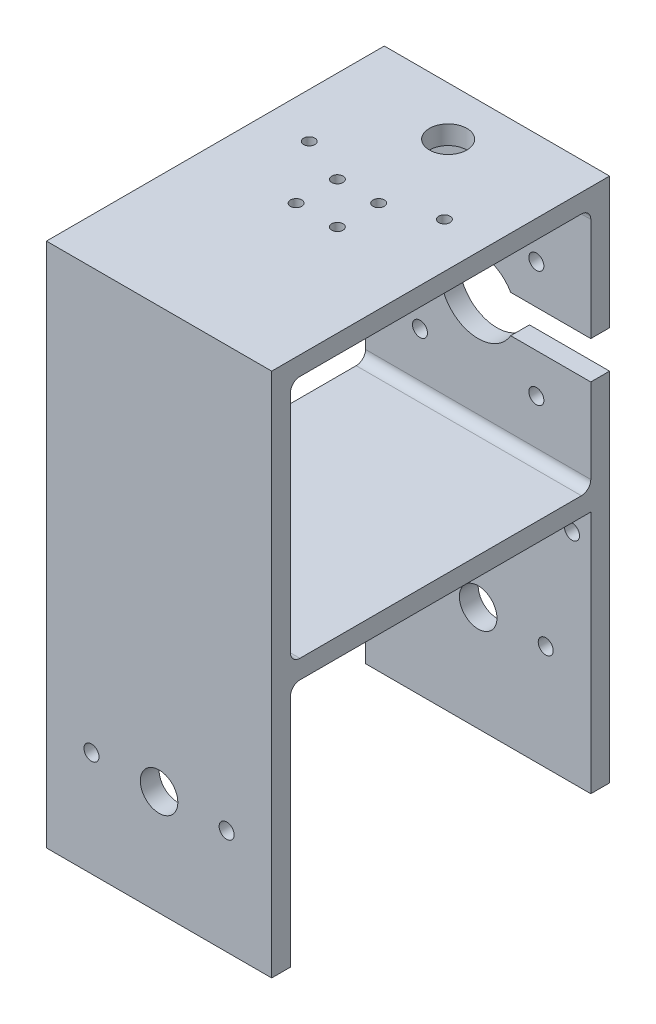
SolidWorks part; units mm, degrees
ref_plane "Front Plane" through (0, 0, 0) normal (0, 0, 1) x (1, 0, 0)
ref_plane "Top Plane" through (0, 0, 0) normal (0, 1, 0) x (1, 0, 0)
ref_plane "Right Plane" through (0, 0, 0) normal (1, 0, 0) x (0, 0, -1)
sketch "Sketch1" plane through (0, 0, 0) normal (1, 0, 0) x (0, 0, -1)
  line L0 (0, 0) -> (0, -140)
  line L1 (0, -140) -> (-5, -140)
  line L2 (-5, -140) -> (-5, -75)
  line L3 (-5, -75) -> (-85, -75)
  line L4 (-85, -75) -> (-85, -140)
  line L5 (-85, -140) -> (-90, -140)
  line L6 (-90, -140) -> (-90, 0)
  line L7 (-90, 0) -> (0, 0)
  dimension "D1" = 90
  dimension "D2" = 80
  dimension "D3" = 5
  dimension "D4" = 80
  dimension "D5" = 65
  dimension "D6" = 65
  dimension "D7" = 75
  dimension "D8" = 140
  dimension "D9" = 5
extrude "Boss-Extrude1" add sketch "Sketch1" against normal blind 60
sketch "Sketch2" plane through (0, 0, 0) normal (1, 0, 0) x (0, 0, -1)
  line L0 (-85, -75) -> (-5, -75) construction
  line L1 (-85, -70) -> (-5, -70)
  line L2 (-85, -70) -> (-85, -5)
  line L3 (-85, -5) -> (-5, -5)
  line L4 (-5, -70) -> (-5, -5)
  line L5 (0, 0) -> (-90, 0) construction
  line L6 (0, -140) -> (0, 0) construction
  line L7 (-90, 0) -> (-90, -140) construction
  dimension "D1" = 5
  dimension "D2" = 5
  dimension "D3" = 5
  dimension "D4" = 5
  dimension "D5" = 65
  dimension "D6" = 80
extrude "Cut-Extrude1" cut sketch "Sketch2" against normal blind 60
sketch "Sketch3" plane through (0, 0, 0) normal (0, 1, 0) x (1, 0, 0)
  line L0 (-30, 0) -> (-30, -90) construction
  line L1 (-60, 0) -> (0, 0) construction
  line L2 (-60, -90) -> (0, -90) construction
  line L3 (-60, -45) -> (0, -45) construction
  line L4 (-60, 0) -> (-60, -90) construction
  line L5 (0, 0) -> (0, -90) construction
  circle A0 centre (-35.5, -37) radius 1.5
  circle A1 centre (-24.5, -37) radius 1.5
  circle A2 centre (-24.5, -48) radius 1.5
  circle A3 centre (-35.5, -48) radius 1.5
  circle A4 centre (-30, -13) radius 5
  circle A5 centre (-12, -32) radius 1.5
  circle A6 centre (-48, -32) radius 1.5
  dimension "D5" = 3
  dimension "D6" = 3
  dimension "D7" = 3
  dimension "D8" = 3
  dimension "D9" = 10
  dimension "D15" = 3
  dimension "D16" = 3
  dimension "D1" = 11
  dimension "D2" = 11
  dimension "D3" = 24.5
  dimension "D4" = 37
  dimension "D10" = 13
  dimension "D11" = 32
  dimension "D12" = 32
  dimension "D13" = 12
  dimension "D14" = 12
extrude "Cut-Extrude2" cut sketch "Sketch3" against normal up to next
sketch "Sketch4" plane through (0, 0, 0) normal (0, 0, 1) x (1, 0, 0)
  line L0 (-30, 0) -> (-30, -140) construction
  line L1 (-60, 0) -> (0, 0) construction
  line L2 (-60, -140) -> (0, -140) construction
  line L4 (0, 0) -> (0, -140) construction
  line L5 (-60, 0) -> (-60, -140) construction
  line L6 (-60, -140) -> (0, -140) construction
  line L11 (0, -70) -> (-60, -70) construction
  line L12 (0, -140) -> (0, 0) construction
  line L13 (-60, -140) -> (-60, 0) construction
  line L14 (-30, -40) -> (0, -40) construction
  line L21 (-14.5, -55.5) -> (-45.5, -24.5) construction
  line L22 (-14.5, -24.5) -> (-45.5, -55.5) construction
  line L23 (-60, 0) -> (0, 0) construction
  circle A0 centre (-30, -112) radius 5
  circle A1 centre (-30, -40) radius 10
  circle A6 centre (-5, -82) radius 2
  circle A7 centre (-55, -82) radius 2
  circle A12 centre (-14.5, -24.5) radius 2
  circle A13 centre (-45.5, -24.5) radius 2
  circle A14 centre (-45.5, -55.5) radius 2
  circle A15 centre (-14.5, -55.5) radius 2
  dimension "D2" = 10
  dimension "D3" = 20
  dimension "D7" = 4
  dimension "D8" = 4
  dimension "D9" = 24.5
  dimension "D10" = 4
  dimension "D19" = 4
  dimension "D20" = 4
  dimension "D11" = 4
  dimension "D4" = 72
  dimension "D5" = 31
  dimension "D6" = 31
  dimension "D13" = 12
  dimension "D14" = 12
  dimension "D15" = 28
  dimension "D16" = 58
  dimension "D17" = 5
  dimension "D18" = 5
  dimension "D21" = 58
extrude "Cut-Extrude3" cut sketch "Sketch4" along normal up to next
fillet "Fillet1" radius 2.5 1 edges at (-30, -75, 85)
fillet "Fillet3" radius 2.5 1 edges at (-30, -70, 85)
fillet "Fillet4" radius 2.5 1 edges at (-30, -70, 5)
fillet "Fillet5" radius 2.5 1 edges at (-30, -5, 5)
fillet "Fillet6" radius 2.5 1 edges at (-30, -5, 85)
sketch "Sketch5" plane through (0, 0, 90) normal (0, 0, 1) x (1, 0, 0)
  line L0 (-30, 0) -> (-30, -140) construction
  line L1 (-60, 0) -> (0, 0) construction
  line L2 (-60, -140) -> (0, -140) construction
  circle A0 centre (-30, -112) radius 5
  circle A1 centre (-12, -112) radius 2
  circle A2 centre (-48, -112) radius 2
  dimension "D2" = 10
  dimension "D5" = 4
  dimension "D6" = 4
  dimension "D1" = 28
  dimension "D3" = 18
  dimension "D4" = 18
extrude "Cut-Extrude4" cut sketch "Sketch5" against normal through all
sketch "Sketch6" plane through (0, 0, 0) normal (0, 0, -1) x (-1, 0, 0)
  line L0 (30, -30) -> (30, -50) construction
  line L2 (0, -45) -> (30, -45)
  line L9 (0, -70) -> (60, -70) construction
  line L11 (0, -45) -> (0, -35)
  line L15 (0, -140) -> (0, 0) construction
  line L16 (60, -140) -> (60, 0) construction
  line L17 (20, -40) -> (40, -40) construction
  line L18 (0, -35) -> (30, -35)
  line L19 (30, -45) -> (30, -35)
  circle A2 centre (30, -40) radius 10 construction
  point P2 (30, -40)
  dimension "D1" = 5
  dimension "D2" = 5
  dimension "D3" = 30
  dimension "D4" = 10
extrude "Cut-Extrude5" cut sketch "Sketch6" against normal up to next
